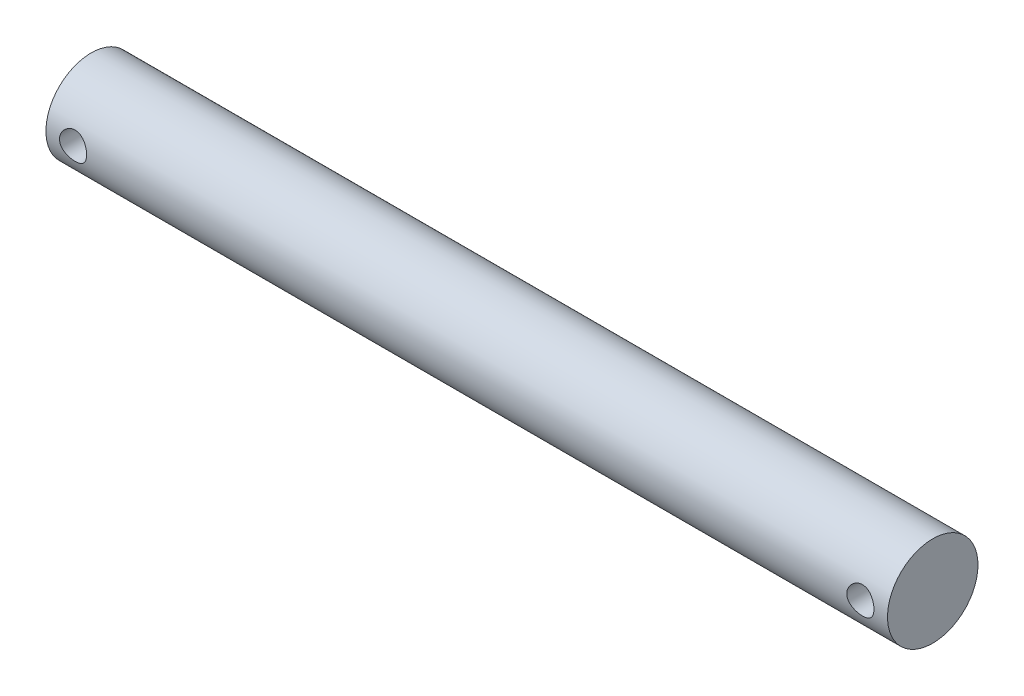
SolidWorks part; units mm, degrees
material "Aleación 1060"
ref_plane "Alzado" through (0, 0, 0) normal (0, 0, 1) x (1, 0, 0)
ref_plane "Planta" through (0, 0, 0) normal (0, 1, 0) x (1, 0, 0)
ref_plane "Vista lateral" through (0, 0, 0) normal (1, 0, 0) x (0, 0, -1)
sketch "Croquis1" plane through (0, 0, 0) normal (1, 0, 0) x (0, 0, -1)
  circle A0 centre (0, 0) radius 5
  dimension "D1" = 10
extrude "Saliente-Extruir1" add sketch "Croquis1" along normal blind 93
sketch "Croquis2" plane through (0, 0, 0) normal (0, 0, 1) x (1, 0, 0)
  line L0 (0, 0) -> (93, 0) construction
  line L1 (93, -5) -> (93, 5) construction
  line L2 (0, 5) -> (0, -5) construction
  circle A0 centre (3, 0) radius 1.5
  circle A1 centre (90, 0) radius 1.5
  dimension "D1" = 3
  dimension "D2" = 3
  dimension "D3" = 3
  dimension "D4" = 3
extrude "Cortar-Extruir1" cut sketch "Croquis2" against normal up to next and the other way up to next
